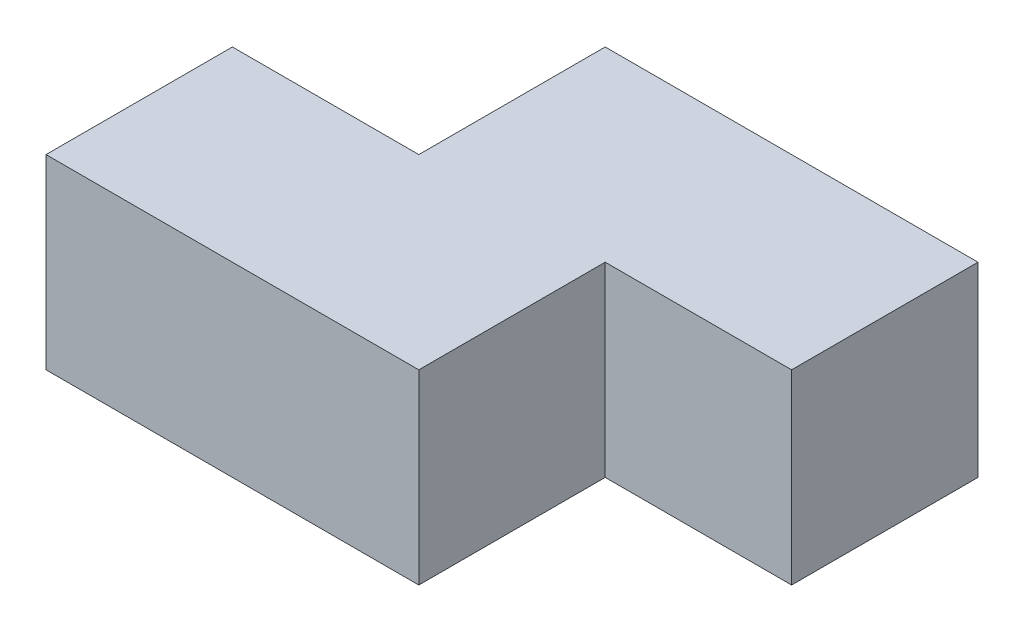
SolidWorks part; units mm, degrees
ref_plane "Alzado" through (0, 0, 0) normal (0, 0, 1) x (1, 0, 0)
ref_plane "Planta" through (0, 0, 0) normal (0, 1, 0) x (1, 0, 0)
ref_plane "Vista lateral" through (0, 0, 0) normal (1, 0, 0) x (0, 0, -1)
sketch "Croquis1" plane through (0, 0, 0) normal (0, 1, 0) x (1, 0, 0)
  line L1 (0, 0) -> (400, 0)
  line L2 (0, 0) -> (0, 200)
  line L3 (0, 200) -> (200, 200)
  line L4 (400, 0) -> (400, 200)
  line L5 (400, 200) -> (600, 200)
  line L6 (200, 200) -> (200, 400)
  line L7 (200, 400) -> (600, 400)
  line L8 (600, 200) -> (600, 400)
  dimension "D1" = 200
  dimension "D2" = 200
  dimension "D3" = 400
  dimension "D4" = 400
  dimension "D5" = 200
  dimension "D6" = 200
extrude "Saliente-Extruir1" add sketch "Croquis1" along normal blind 200
